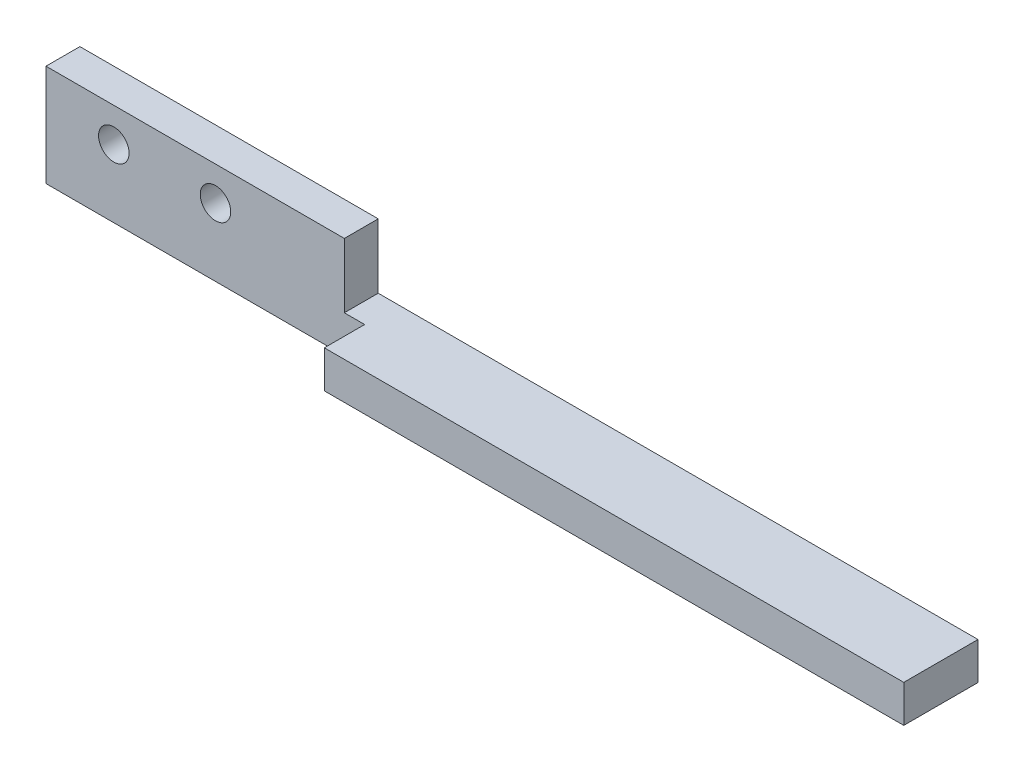
SolidWorks part; units mm, degrees
ref_plane "前视基准面" through (0, 0, 0) normal (0, 0, 1) x (1, 0, 0)
ref_plane "上视基准面" through (0, 0, 0) normal (0, 1, 0) x (1, 0, 0)
ref_plane "右视基准面" through (0, 0, 0) normal (1, 0, 0) x (0, 0, -1)
sketch "草图1" plane through (0, 0, 0) normal (0, 0, 1) x (1, 0, 0)
  line L1 (0, 0) -> (100, 0)
  line L2 (0, 0) -> (0, 25)
  line L3 (0, 25) -> (100, 25)
  line L4 (100, 0) -> (100, 25)
  dimension "D1" = 100
  dimension "D2" = 25
extrude "凸台-拉伸1" add sketch "草图1" along normal blind 5
sketch "草图2" plane through (0, 0, 0) normal (0, -1, 0) x (1, 0, 0)
  line L0 (0, 5) -> (100, 5) construction
  line L1 (100, 0) -> (47, 0)
  line L2 (100, 0) -> (100, 5)
  line L3 (100, 5) -> (47, 5)
  line L4 (47, 0) -> (47, 5)
  dimension "D1" = 53
extrude "凸台-拉伸2" add sketch "草图2" along normal blind 5
sketch "草图5" plane through (0, 25, 0) normal (0, 1, 0) x (1, 0, 0)
  line L0 (100, 0) -> (0, 0) construction
  line L1 (100, -5) -> (44, -5)
  line L2 (100, -5) -> (100, 0)
  line L3 (100, 0) -> (44, 0)
  line L4 (44, -5) -> (44, 0)
  dimension "D1" = 56
extrude "切除-拉伸1" cut sketch "草图5" against normal blind 10
sketch "草图6" plane through (47, 0, 0) normal (-1, 0, 0) x (0, 0, 1)
  line L1 (5, -5) -> (0, -5)
  line L2 (5, -5) -> (5, 0)
  line L3 (5, 0) -> (0, 0)
  line L4 (0, -5) -> (0, 0)
extrude "凸台-拉伸3" add sketch "草图6" along normal up to surface (47 mm away) up to face at (0, 12.5, 2.5)
sketch "草图7" plane through (0, 15, 0) normal (0, 1, 0) x (1, 0, 0)
  line L1 (44, 0) -> (100, 0)
  line L2 (44, 0) -> (44, -5)
  line L3 (44, -5) -> (100, -5)
  line L4 (100, 0) -> (100, -5)
extrude "切除-拉伸2" cut sketch "草图7" against normal blind 14.5
sketch "草图8" plane through (0, 0, 5) normal (0, 0, 1) x (1, 0, 0)
  line L0 (44, 0.5) -> (100, 0.5) construction
  line L1 (100, -5) -> (47, -5)
  line L2 (100, -5) -> (100, 0.5)
  line L3 (100, 0.5) -> (47, 0.5)
  line L4 (47, -5) -> (47, 0.5)
  dimension "D1" = 53
extrude "凸台-拉伸4" add sketch "草图8" along normal blind 5.95
sketch "草图9" plane through (100, 0, 0) normal (1, 0, 0) x (0, 0, -1)
  line L1 (0, 0.5) -> (-10.95, 0.5)
  line L2 (0, 0.5) -> (0, -5)
  line L3 (0, -5) -> (-10.95, -5)
  line L4 (-10.95, 0.5) -> (-10.95, -5)
extrude "凸台-拉伸5" add sketch "草图9" along normal blind 32.46
sketch "草图11" plane through (0, 25, 0) normal (0, 1, 0) x (1, 0, 0)
  line L1 (0, 0) -> (44, 0)
  line L2 (0, 0) -> (0, -5)
  line L3 (0, -5) -> (44, -5)
  line L4 (44, 0) -> (44, -5)
extrude "切除-拉伸3" cut sketch "草图11" against normal blind 15
sketch "草图12" plane through (0, 0, 0) normal (0, 0, -1) x (-1, 0, 0)
  line L1 (-44, 10) -> (0, 10) construction
  line L2 (0, 10) -> (0, -5) construction
  circle A0 centre (-10, 5) radius 2.25
  circle A1 centre (-25, 5) radius 2.25
  dimension "D1" = 5
  dimension "D3" = 4.5
  dimension "D2" = 10
  dimension "D4" = 15
extrude "切除-拉伸4" cut sketch "草图12" against normal blind 15
